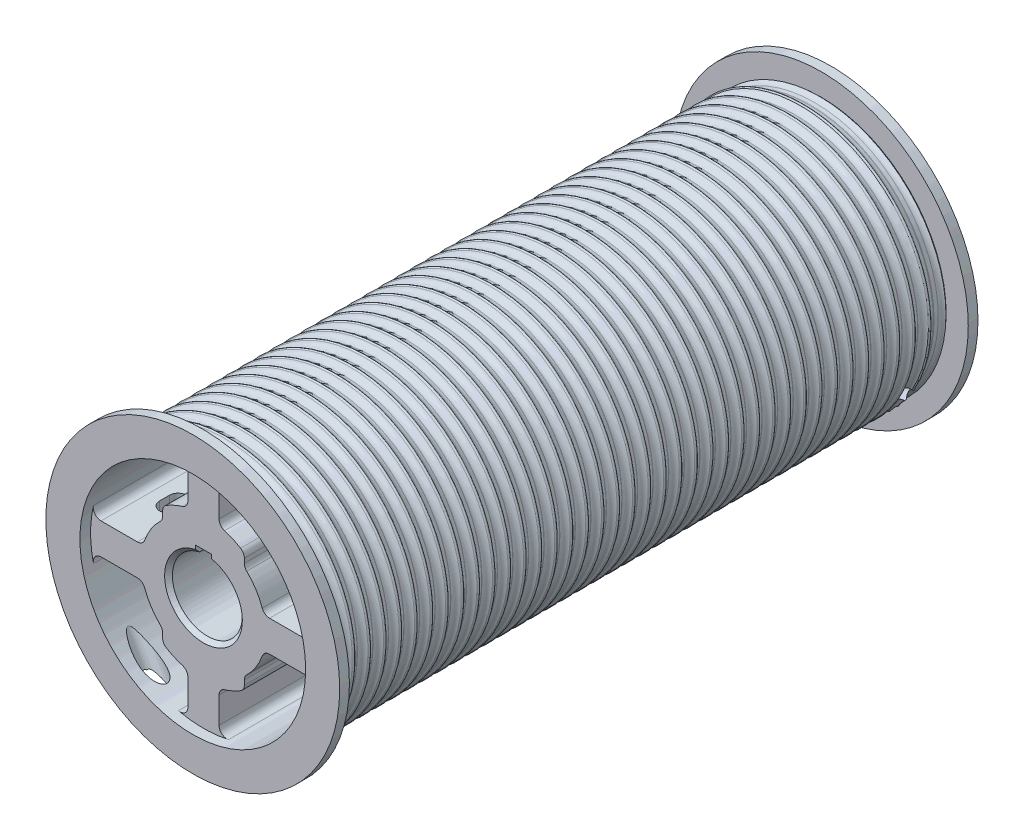
SolidWorks part; units mm, degrees
ref_plane "Front" through (0, 0, 0) normal (0, 0, 1) x (1, 0, 0)
ref_plane "Top" through (0, 0, 0) normal (0, 1, 0) x (1, 0, 0)
ref_plane "Right" through (0, 0, 0) normal (1, 0, 0) x (0, 0, -1)
ref_plane "Plane1" through (0, 0, 0) normal (0, 0, 1) x (1, 0, 0)
ref_plane "Plane2" through (0, 0, 0) normal (0, 1, 0) x (-1, 0, 0)
ref_plane "Plane3" through (0, 0, 0) normal (1, 0, 0) x (0, 0, -1)
ref_plane "END PLANE" through (0, 0, -520.7) normal (0, 0, 1) x (1, 0, 0)
sketch "Sketch1" plane through (0, 0, 0) normal (0, 0, 1) x (1, 0, 0)
  line L0 (-12.7, 62.2373) -> (-12.7, 83.5815)
  line L1 (12.7, 62.2373) -> (12.7, 83.5815)
  line L2 (-53.9085, -12.7) -> (-83.5815, -12.7)
  line L3 (-53.9085, 12.7) -> (-83.5815, 12.7)
  line L4 (-12.7, -62.2373) -> (-12.7, -83.5815)
  line L5 (12.7, -62.2373) -> (12.7, -83.5815)
  line L6 (-33.3375, 41.1574) -> (-33.3375, 44.9013)
  line L7 (-33.3375, -41.1574) -> (-33.3375, -44.9013)
  line L8 (53.9085, 12.7) -> (83.5815, 12.7)
  line L9 (33.3375, 41.1574) -> (33.3375, 44.9013)
  line L10 (53.9085, -12.7) -> (83.5815, -12.7)
  line L11 (33.3375, -41.1574) -> (33.3375, -44.9013)
  arc A0 (30.2587, -50.3439) -> (33.3375, -44.9013) centre (26.9875, -44.9013) ccw
  arc A1 (33.3375, 44.9013) -> (30.2587, 50.3439) centre (26.9875, 44.9013) ccw
  arc A2 (-17.1915, 56.1654) -> (-12.7, 62.2373) centre (-19.05, 62.2373) ccw
  arc A3 (-35.2797, 36.5864) -> (-47.9213, 16.9343) centre (0, 0) ccw
  arc A4 (-35.2797, 36.5864) -> (-47.9213, 16.9343) centre (0, 0) ccw
  arc A5 (-17.1915, 56.1654) -> (-30.2587, 50.3439) centre (0, 0) ccw
  arc A6 (-35.2797, 36.5864) -> (-33.3375, 41.1574) centre (-39.6875, 41.1574) ccw
  arc A7 (-30.2587, 50.3439) -> (-33.3375, 44.9013) centre (-26.9875, 44.9013) ccw
  arc A8 (-53.9085, 12.7) -> (-47.9213, 16.9343) centre (-53.9085, 19.05) ccw
  arc A9 (12.7, 62.2373) -> (17.1915, 56.1654) centre (19.05, 62.2373) ccw
  arc A10 (30.2587, 50.3439) -> (17.1915, 56.1654) centre (0, 0) ccw
  arc A11 (30.2587, 50.3439) -> (17.1915, 56.1654) centre (0, 0) ccw
  arc A12 (-12.7, -62.2373) -> (-17.1915, -56.1654) centre (-19.05, -62.2373) ccw
  arc A13 (-47.9213, -16.9343) -> (-53.9085, -12.7) centre (-53.9085, -19.05) ccw
  arc A14 (-47.9213, -16.9343) -> (-35.2797, -36.5864) centre (0, 0) ccw
  arc A15 (-33.3375, -41.1574) -> (-35.2797, -36.5864) centre (-39.6875, -41.1574) ccw
  arc A16 (-33.3375, -44.9013) -> (-30.2587, -50.3439) centre (-26.9875, -44.9013) ccw
  arc A17 (-30.2587, -50.3439) -> (-17.1915, -56.1654) centre (0, 0) ccw
  arc A18 (17.1915, -56.1654) -> (12.7, -62.2373) centre (19.05, -62.2373) ccw
  arc A19 (17.1915, -56.1654) -> (30.2587, -50.3439) centre (0, 0) ccw
  arc A20 (47.9213, 16.9343) -> (35.2797, 36.5864) centre (0, 0) ccw
  arc A21 (47.9213, 16.9343) -> (35.2797, 36.5864) centre (0, 0) ccw
  arc A22 (33.3375, 41.1574) -> (35.2797, 36.5864) centre (39.6875, 41.1574) ccw
  arc A23 (47.9213, 16.9343) -> (53.9085, 12.7) centre (53.9085, 19.05) ccw
  arc A24 (53.9085, -12.7) -> (47.9213, -16.9343) centre (53.9085, -19.05) ccw
  arc A25 (35.2797, -36.5864) -> (33.3375, -41.1574) centre (39.6875, -41.1574) ccw
  arc A26 (35.2797, -36.5864) -> (47.9213, -16.9343) centre (0, 0) ccw
  arc A27 (-20.4611, 89.7728) -> (-89.7728, 20.4611) centre (0, 0) ccw
  arc A28 (-12.7, 83.5815) -> (-20.4611, 89.7728) centre (-19.05, 83.5815) ccw
  arc A29 (-89.7728, 20.4611) -> (-83.5815, 12.7) centre (-83.5815, 19.05) ccw
  arc A30 (-89.7728, -20.4611) -> (-20.4611, -89.7728) centre (0, 0) ccw
  arc A31 (-83.5815, -12.7) -> (-89.7728, -20.4611) centre (-83.5815, -19.05) ccw
  arc A32 (-20.4611, -89.7728) -> (-12.7, -83.5815) centre (-19.05, -83.5815) ccw
  arc A33 (20.4611, -89.7728) -> (89.7728, -20.4611) centre (0, 0) ccw
  arc A34 (12.7, -83.5815) -> (20.4611, -89.7728) centre (19.05, -83.5815) ccw
  arc A35 (89.7728, -20.4611) -> (83.5815, -12.7) centre (83.5815, -19.05) ccw
  arc A36 (89.7728, 20.4611) -> (20.4611, 89.7728) centre (0, 0) ccw
  arc A37 (83.5815, 12.7) -> (89.7728, 20.4611) centre (83.5815, 19.05) ccw
  arc A38 (20.4611, 89.7728) -> (12.7, 83.5815) centre (19.05, 83.5815) ccw
  circle A39 centre (0, 0) radius 100.8063
extrude "Extrude1" add sketch "Sketch1" against normal up to surface (520.7 mm away) contours A39 A29 A27 A28 L0 A2 A5 A7 L6 A6 A3 A8 L3 A32 A30 A31 L2 A13 A14 A15 L7 A16 A17 A12 L4 A35 A33 A34 L5 A18 A19 A0 L11 A25 A26 A24 L10 A38 A36 A37 L8 A23 A20 A22 L9 A1 A10 up to plane "END PLANE"
sketch "Sketch2" plane through (0, 0, 0) normal (0, 0, 1) x (1, 0, 0)
  circle A0 centre (0, 0) radius 119.8563
  circle A1 centre (0, 0) radius 100.8063
  dimension "D1" = 239.7125
  dimension "D2" = 201.6125
extrude "Extrude2" add sketch "Sketch2" against normal blind 7.9375
sketch "Sketch3" plane through (0, 0, -520.7) normal (0, 0, 1) x (1, 0, 0)
  circle A0 centre (0, 0) radius 119.8563
  circle A1 centre (0, 0) radius 100.8063
  dimension "D1" = 239.7125
  dimension "D2" = 201.6125
extrude "Extrude3" add sketch "Sketch3" along normal blind 7.9375
sketch "Sketch4" plane through (0, 0, -520.7) normal (0, 0, 1) x (1, 0, 0)
  circle A0 centre (0, 0) radius 27.0066
  dimension "D1" = 54.0131
extrude "Cut-Extrude1" cut sketch "Sketch4" along normal through all
sketch "Sketch5" plane through (0, 0, 0) normal (0, 0, 1) x (1, 0, 0)
  line L0 (6.35, 27.8149) -> (6.35, 34.2157)
  line L1 (-6.35, 27.8149) -> (-6.35, 34.2157)
  line L2 (-6.35, 34.2157) -> (6.35, 34.2157)
  arc A0 (-6.35, 27.8149) -> (6.35, 27.8149) centre (0, 0) ccw
  dimension "D1" = 28.5306
extrude "Cut-Extrude2" cut sketch "Sketch5" against normal blind 88.9
sketch "Sketch6" plane through (0, 0, 0) normal (0, 0, 1) x (1, 0, 0)
  circle A0 centre (0, 0) radius 92.075
  dimension "D1" = 184.15
extrude "Cut-Extrude3" cut sketch "Sketch6" against normal blind 8.7312
sketch "Sketch7" plane through (0, 0, -520.7) normal (0, 0, 1) x (1, 0, 0)
  circle A0 centre (0, 0) radius 92.075
  dimension "D1" = 184.15
extrude "Cut-Extrude4" cut sketch "Sketch7" along normal blind 8.7312
sketch "Sketch8" plane through (0, 0, 0) normal (1, 0, 0) x (0, 0, -1)
  line L0 (7.9375, 100.8063) -> (20.8626, 100.8063)
  line L1 (0, 50) -> (0, -50) construction
  line L2 (50, 0) -> (-50, 0) construction
  arc A0 (7.9375, 100.8063) -> (13.3758, 104.1102) centre (8.05, 106.7488) ccw
  arc A1 (15.4242, 104.1102) -> (20.8626, 100.8063) centre (20.75, 106.7488) ccw
  arc A2 (15.4242, 104.1102) -> (13.3758, 104.1102) centre (14.4, 103.6028) ccw
  dimension "D1" = 5.9436
  dimension "D2" = 5.9436
  dimension "D3" = 1.143
  dimension "D4" = 7.9375
  dimension "D5" = 100.8063
revolve "Revolve1" add sketch "Sketch8" angle 360 about axis through (0, 0, -805.8231) along (0, 0, 1)
pattern_linear "LPattern1" count 40 spacing 12.7 along (0, 0, -1) of "Revolve1"
sketch "Sketch9" plane through (0, 0, 0) normal (1, 0, 0) x (0, 0, -1)
  line L0 (13.4209, 100.8063) -> (16.821, 100.8063)
  line L1 (7.9375, 104.7458) -> (22.3043, 104.7458)
  line L3 (503.879, 100.8101) -> (507.2791, 100.8101)
  line L4 (498.3957, 104.7496) -> (512.7625, 104.7496)
  line L5 (0, 50) -> (0, -50) construction
  line L8 (50, 0) -> (-50, 0) construction
  line L11 (520.7, 50) -> (520.7, -50) construction
  arc A0 (7.9375, 104.7458) -> (13.4209, 100.8063) centre (13.5334, 106.7488) ccw
  arc A1 (16.821, 100.8063) -> (22.3043, 104.7458) centre (16.7084, 106.7488) ccw
  arc A2 (498.3957, 104.7496) -> (503.879, 100.8101) centre (503.9916, 106.7526) ccw
  arc A3 (507.2791, 100.8101) -> (512.7625, 104.7496) centre (507.1666, 106.7526) ccw
  dimension "D1" = 5.9436
  dimension "D2" = 5.9436
  dimension "D14" = 5.9436
  dimension "D15" = 5.9436
  dimension "D3" = 3.9395
  dimension "D4" = 14.3668
  dimension "D5" = 7.9375
  dimension "D6" = 3.175
  dimension "D7" = 13.5334
  dimension "D9" = 104.7458
  dimension "D10" = 14.3668
  dimension "D11" = 7.9375
  dimension "D12" = 3.175
  dimension "D13" = 3.9395
  dimension "D17" = 13.5334
  dimension "D18" = 104.7496
revolve "Cut-Revolve1" cut sketch "Sketch9" angle 360 about axis through (0, 0, -805.8231) along (0, 0, 1)
ref_plane "Plane6" through (0, 0, 0) normal (-0.4924, 0.8704, 0) x (-0.8704, -0.4924, 0)
sketch "Sketch10" plane through (0, 0, 0) normal (-0.4924, 0.8704, 0) x (-0.8704, -0.4924, 0)
  line L0 (50, 0) -> (-50, 0) construction
  line L1 (0, -511.9688) -> (0, -8.7312) construction
  circle A0 centre (82.55, -17.4625) radius 7.9375
  dimension "D1" = 15.875
  dimension "D2" = 17.4625
  dimension "D3" = 82.55
extrude "Cut-Extrude5" cut sketch "Sketch10" against normal up to next
chamfer "Chamfer1" distance 3.175 angle 45 2 edges at (27.0066, 0, -511.9688) (0, -28.5306, -8.7312)
ref_plane "Plane7" through (0, 0, 0) normal (-0.8387, 0.5446, 0) x (0, 0, 1)
ref_plane "Plane9" through (84.5432, -54.903, 0) normal (-0.8387, 0.5446, 0) x (-0.5446, -0.8387, 0)
sketch "Sketch39" plane through (0, 0, 0) normal (-0.8387, 0.5446, 0) x (0, 0, 1)
  line L0 (-20.8626, 0) -> (-20.6375, 0) construction
  point P0 (-290.8026, 0)
hole_wizard "1/2-13 Tapped Hole6" positions "Sketch43" profile "Sketch42" tap size "1/2-13" standard "Ansi Inch"
sketch "Sketch43" plane through (84.5432, -54.903, 0) normal (-0.8387, 0.5446, 0) x (-0.5446, -0.8387, 0)
  line L0 (0, -512.7625) -> (0, -520.7) construction
  line L2 (0, -20.8626) -> (0, -20.6375) construction
  line L3 (50, -520.7) -> (-50, -520.7) construction
  point P0 (0, -493.7125)
  dimension "D1" = 26.9875
sketch "Sketch42" plane through (84.5432, -54.903, -493.7125) normal (0, 0, 1) x (0.5446, 0.8387, 0)
  line L0 (0, 0) -> (0, 104.8195)
  line L1 (0, 104.8195) -> (5.3581, 101.6)
  line L2 (5.3581, 101.6) -> (5.3581, 25.4)
  line L3 (5.3581, 25.4) -> (6.35, 25.4)
  line L4 (6.35, 25.4) -> (6.35, 0)
  line L5 (6.35, 0) -> (0, 0)
  line L10 (0, 104.8195) -> (-5.3581, 101.6) construction
  line L11 (0, -6.35) -> (0, 107.95) construction
  dimension "Tap Drill Dia." = 10.7163
  dimension "Tap Drill Depth" = 101.6
  dimension "Thread Major Dia." = 12.7
  dimension "Thread Depth" = 25.4
  dimension "Drill Angle" = 118
sketch "Sketch44" plane through (84.5432, -54.903, 0) normal (-0.8387, 0.5446, 0) x (-0.5446, -0.8387, 0)
  line L0 (0, -20.8626) -> (0, -20.6375) construction
  line L1 (50, -520.7) -> (-50, -520.7) construction
  circle A0 centre (0, -493.7125) radius 6.7469
  dimension "D1" = 13.4937
  dimension "D2" = 26.9875
extrude "17/32 DRILL" cut sketch "Sketch44" along normal up to next and the other way through all
sketch "Sketch45" plane through (0, 0, 0) normal (1, 0, 0) x (0, 0, -1)
  line L0 (435.77, 0) -> (435.77, 39.6875)
  line L1 (50, 0) -> (-50, 0) construction
  line L2 (84.93, 0) -> (84.93, 39.6875)
  line L3 (84.93, 39.6875) -> (239.9907, 72.7459)
  line L4 (242.6388, 73.025) -> (278.0612, 73.025)
  line L5 (280.7093, 72.7459) -> (435.77, 39.6875)
  line L6 (84.93, 0) -> (435.77, 0)
  line L7 (520.7, 50) -> (520.7, -50) construction
  line L8 (0, 50) -> (0, -50) construction
  arc A0 (239.9907, 72.7459) -> (242.6388, 73.025) centre (242.6388, 60.325) cw
  arc A1 (280.7093, 72.7459) -> (278.0612, 73.025) centre (278.0612, 60.325) ccw
  point P14 (241.3, 73.025)
  point P17 (279.4, 73.025)
  dimension "D8" = 12.7
  dimension "D9" = 12.7
  dimension "D1" = 84.93
  dimension "D2" = 84.93
  dimension "D3" = 241.3
  dimension "D4" = 241.3
  dimension "D5" = 73.025
  dimension "D6" = 39.6875
  dimension "D7" = 39.6875
revolve "Cut-Revolve2" cut sketch "Sketch45" angle 360 about axis through (0, 0, -805.8231) along (0, 0, 1)
sketch "Sketch46" plane through (0, 0, 0) normal (0, 1, 0) x (-1, 0, 0)
  line L0 (-59.5312, -46.8312) -> (-59.5312, -54.7687)
  line L1 (-73.8187, -46.8313) -> (-73.8187, -54.7687)
  line L2 (0, 50) -> (0, -50) construction
  line L3 (119.8563, 0) -> (-119.8563, 0) construction
  line L4 (-59.5312, -465.9249) -> (-59.5312, -473.8624)
  line L5 (-73.8187, -465.9249) -> (-73.8187, -473.8624)
  line L6 (50, -520.7) -> (-50, -520.7) construction
  arc A0 (-73.8187, -54.7687) -> (-59.5312, -54.7687) centre (-66.675, -54.7687) ccw
  arc A1 (-59.5312, -46.8312) -> (-73.8187, -46.8313) centre (-66.675, -46.8312) ccw
  arc A2 (-73.8187, -473.8624) -> (-59.5312, -473.8624) centre (-66.675, -473.8624) ccw
  arc A3 (-59.5312, -465.9249) -> (-73.8187, -465.9249) centre (-66.675, -465.9249) ccw
  dimension "D1" = 14.2875
  dimension "D2" = 66.675
  dimension "D4" = 7.9375
  dimension "D9" = 7.1437
  dimension "D3" = 46.8312
  dimension "D5" = 14.2875
  dimension "D6" = 66.675
  dimension "D7" = 46.8376
  dimension "D8" = 7.9375
  dimension "D10" = 14.2875
extrude "Cut-Extrude7" cut sketch "Sketch46" against normal up to next and the other way up to next
mirror "Mirror1" about plane through (0, 0, 0) normal (1, 0, 0) of "Cut-Extrude7"
